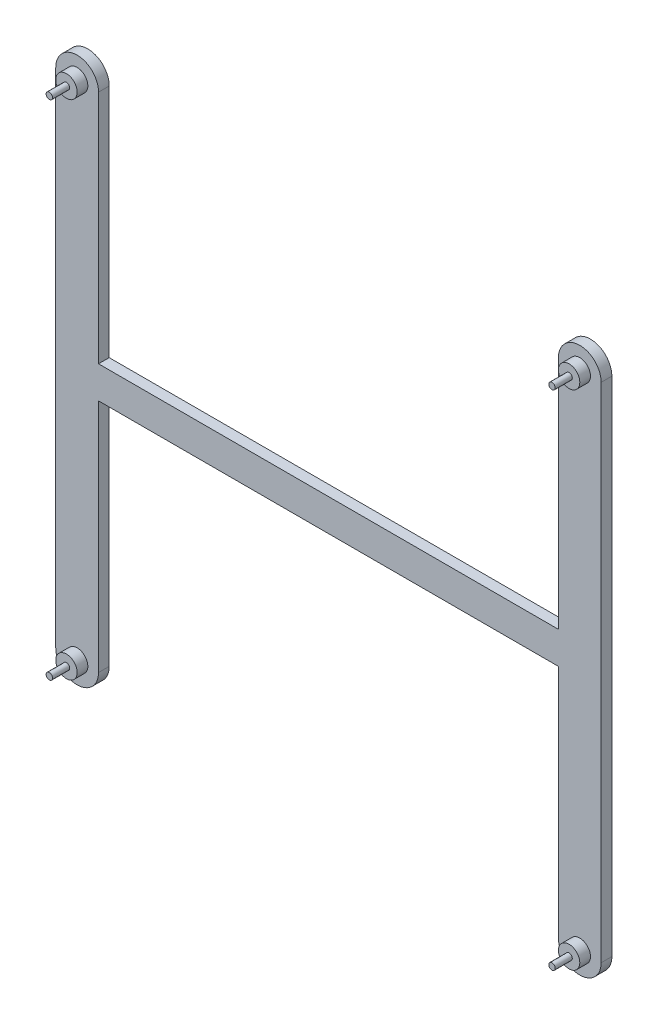
SolidWorks part; units mm, degrees
ref_plane "Front Plane" through (0, 0, 0) normal (0, 0, 1) x (1, 0, 0)
ref_plane "Top Plane" through (0, 0, 0) normal (0, 1, 0) x (1, 0, 0)
ref_plane "Right Plane" through (0, 0, 0) normal (1, 0, 0) x (0, 0, -1)
sketch "Sketch1" plane through (0, 0, 0) normal (0, 0, 1) x (1, 0, 0)
  line L0 (-117.5, 117.5) -> (-117.5, -117.5) construction
  line L1 (-107.5, 7.5) -> (107.5, 7.5)
  line L3 (-107.5, -7.5) -> (107.5, -7.5)
  line L5 (-107.5, -7.5) -> (-107.5, -117.5)
  line L6 (107.5, -7.5) -> (107.5, -117.5)
  line L7 (-107.5, 117.5) -> (-107.5, 7.5)
  line L8 (-127.5, 117.5) -> (-127.5, -117.5)
  line L9 (117.5, 117.5) -> (117.5, -117.5) construction
  line L10 (127.5, 117.5) -> (127.5, -117.5)
  line L11 (107.5, 117.5) -> (107.5, 7.5)
  line L12 (-127.5, 117.5) -> (-107.5, 117.5) construction
  line L13 (-127.5, -117.5) -> (-107.5, -117.5) construction
  line L14 (107.5, 117.5) -> (127.5, 117.5) construction
  line L15 (107.5, -117.5) -> (127.5, -117.5) construction
  line L16 (-117.5, 0) -> (117.5, 0) construction
  line L17 (0, 7.5) -> (0, -7.5) construction
  arc A0 (-107.5, 117.5) -> (-127.5, 117.5) centre (-117.5, 117.5) ccw
  arc A1 (-127.5, -117.5) -> (-107.5, -117.5) centre (-117.5, -117.5) ccw
  arc A2 (127.5, 117.5) -> (107.5, 117.5) centre (117.5, 117.5) ccw
  arc A3 (107.5, -117.5) -> (127.5, -117.5) centre (117.5, -117.5) ccw
  point P1 (0, 0)
  point P8 (-117.5, 0)
  point P15 (117.5, 0)
  dimension "D1" = 7.5
  dimension "D2" = 235
  dimension "D3" = 15
  dimension "D4" = 235
  dimension "D5" = 117.5
  dimension "D6" = 117.5
  dimension "D7" = 20
  dimension "D8" = 20
extrude "Boss-Extrude1" add sketch "Sketch1" along normal blind 5
ref_plane "Plane1" through (0, 0, 5) normal (0, 0, 1) x (1, 0, 0)
sketch "Sketch3" plane through (0, 0, 5) normal (0, 0, 1) x (1, 0, 0)
  line L0 (107.5, -117.5) -> (127.5, -117.5) construction
  circle A0 centre (117.5, -117.5) radius 5
  circle A1 centre (117.5, 117.5) radius 5
  circle A2 centre (-117.5, 117.5) radius 5
  circle A3 centre (-117.5, -117.5) radius 5
  dimension "D1" = 10
  dimension "D2" = 10
  dimension "D3" = 10
  dimension "D4" = 10
extrude "Boss-Extrude2" add sketch "Sketch3" along normal blind 5
ref_plane "Plane2" through (0, 0, 10) normal (0, 0, 1) x (1, 0, 0)
sketch "Sketch4" plane through (0, 0, 10) normal (0, 0, 1) x (1, 0, 0)
  circle A0 centre (-117.5, 117.5) radius 1.5
  circle A1 centre (-117.5, -117.5) radius 1.5
  circle A2 centre (117.5, -117.5) radius 1.5
  circle A3 centre (117.5, 117.5) radius 1.5
  dimension "D1" = 3
  dimension "D2" = 3
  dimension "D3" = 3
  dimension "D4" = 3
extrude "Boss-Extrude3" add sketch "Sketch4" along normal blind 8
